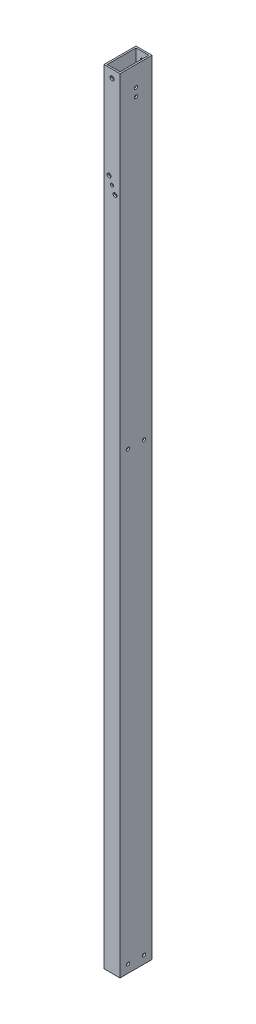
SolidWorks part; units mm, degrees
material "6061-T6 (SS)"
ref_plane "Front Plane" through (0, 0, 0) normal (0, 0, 1) x (1, 0, 0)
ref_plane "Top Plane" through (0, 0, 0) normal (0, 1, 0) x (1, 0, 0)
ref_plane "Right Plane" through (0, 0, 0) normal (1, 0, 0) x (0, 0, -1)
sketch "Sketch1" plane through (0, 0, 0) normal (0, 1, 0) x (1, 0, 0)
  line L1 (0, 0) -> (25.4, 0)
  line L2 (0, 0) -> (0, 50.8)
  line L3 (0, 50.8) -> (25.4, 50.8)
  line L4 (25.4, 0) -> (25.4, 50.8)
  dimension "D1" = 25.4
  dimension "D2" = 50.8
extrude "Extrude-Thin1" add sketch "Sketch1" along normal blind 1244.6 thin thin type one direction reverse wall 2.54
sketch "Sketch2" plane through (25.4, 0, 0) normal (1, 0, 0) x (0, 0, -1)
  circle A0 centre (25.4, 1200.15) radius 2.4892 construction
  circle A1 centre (25.4, 1212.85) radius 2.4892 construction
  circle A2 centre (25.4, 1200.15) radius 2.4892
  circle A3 centre (25.4, 1212.85) radius 2.4892
extrude "Cut-Extrude1" cut sketch "Sketch2" against normal through all
sketch "Sketch3" plane through (0, 0, 0) normal (-1, 0, 0) x (0, 0, 1)
  circle A7 centre (-12.7, 721.6321) radius 2.5019 construction
  circle A8 centre (-38.1, 721.6321) radius 2.5019 construction
  circle A9 centre (-12.7, 12.9602) radius 2.4892 construction
  circle A10 centre (-38.1, 12.7) radius 2.4892 construction
  circle A18 centre (-12.7, 721.6321) radius 2.5019
  circle A19 centre (-38.1, 721.6321) radius 2.5019
  circle A20 centre (-12.7, 12.9602) radius 2.4892
  circle A21 centre (-38.1, 12.7) radius 2.4892
extrude "Cut-Extrude2" cut sketch "Sketch3" against normal through all
sketch "Sketch5" plane through (0, 0, -50.8) normal (0, 0, -1) x (-1, 0, 0)
  line L0 (-25.4, 1244.6) -> (0, 1244.6) construction
  line L1 (0, 1244.6) -> (0, 0) construction
  circle A0 centre (-12.7, 1084.8046) radius 2.4892
  dimension "D1" = 159.7954
  dimension "D3" = 4.9784
  dimension "D2" = 12.7
extrude "Cut-Extrude3" cut sketch "Sketch5" against normal through all
sketch "Sketch6" plane through (0, 0, -50.8) normal (0, 0, -1) x (-1, 0, 0)
  line L0 (-25.4, 1244.6) -> (0, 1244.6) construction
  line L1 (0, 1244.6) -> (0, 0) construction
  circle A0 centre (-12.7, 1231.9) radius 3.175
  dimension "D1" = 12.7
  dimension "D3" = 6.35
  dimension "D2" = 12.7
extrude "Cut-Extrude4" cut sketch "Sketch6" against normal through all
sketch "Sketch7" plane through (0, 0, 0) normal (0, 0, 1) x (1, 0, 0)
  line L0 (25.4, 1244.6) -> (25.4, 0) construction
  line L1 (0, 1103.8546) -> (25.4, 1103.8546) construction
  line L2 (0, 1244.6) -> (0, 0) construction
  line L3 (0, 1065.7546) -> (25.4, 1065.7546) construction
  line L4 (7.9375, 1095.9171) -> (17.4625, 1073.6921) construction
  circle A0 centre (7.9375, 1095.9171) radius 3.175
  circle A1 centre (17.4625, 1073.6921) radius 3.175
  circle A2 centre (12.7, 1084.8046) radius 2.4892 construction
  circle A3 centre (12.7, 1084.8046) radius 2.4892 construction
  dimension "D1" = 6.35
  dimension "D3" = 38.1
  dimension "D4" = 7.9375
  dimension "D5" = 7.9375
  dimension "D2" = 7.9375
  dimension "D6" = 7.9375
extrude "Cut-Extrude5" cut sketch "Sketch7" against normal through all
equation "\"D4@Sketch7\"=\"D2@Sketch7\""
equation "\"D5@Sketch7\"=\"D2@Sketch7\""
equation "\"D6@Sketch7\"=\"D2@Sketch7\""
